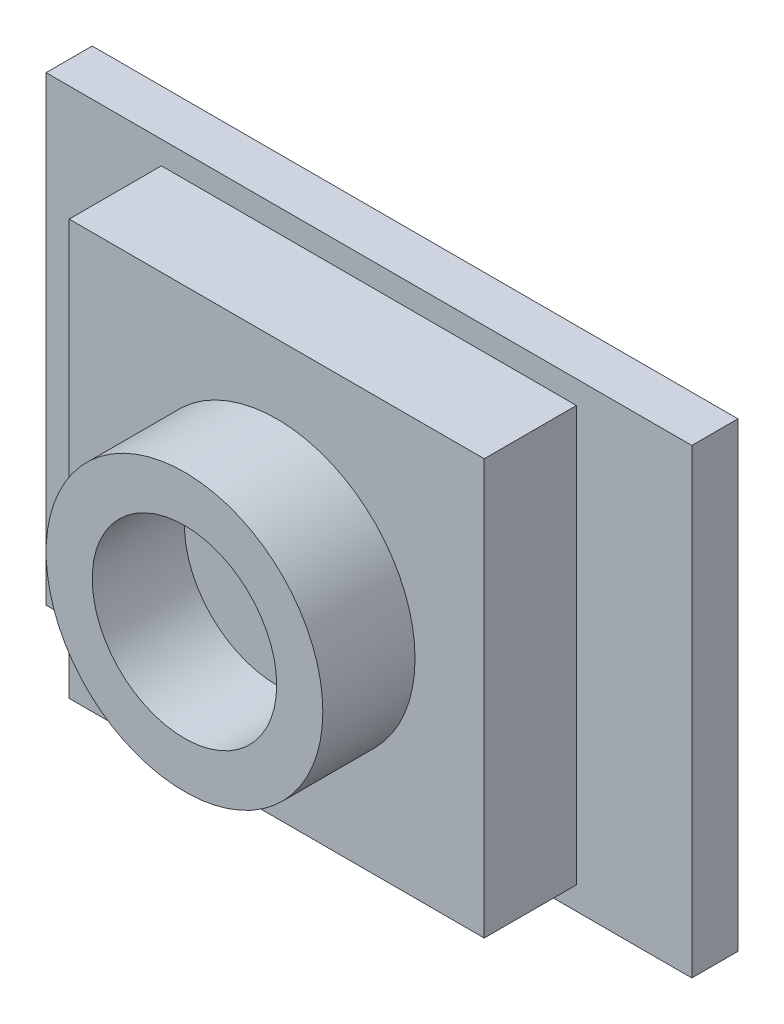
SolidWorks part; units mm, degrees
ref_plane "Front Plane" through (0, 0, 0) normal (0, 0, 1) x (1, 0, 0)
ref_plane "Top Plane" through (0, 0, 0) normal (0, 1, 0) x (1, 0, 0)
ref_plane "Right Plane" through (0, 0, 0) normal (1, 0, 0) x (0, 0, -1)
sketch "Sketch1" plane through (0, 0, 0) normal (0, 0, 1) x (1, 0, 0)
  line L1 (-44.45, -31.75) -> (44.45, -31.75)
  line L2 (-44.45, -31.75) -> (-44.45, 31.75)
  line L3 (-44.45, 31.75) -> (44.45, 31.75)
  line L4 (44.45, -31.75) -> (44.45, 31.75)
  line L5 (-44.45, -31.75) -> (44.45, 31.75) construction
  line L6 (-44.45, 31.75) -> (44.45, -31.75) construction
  line L7 (-28.575, -28.575) -> (28.575, -28.575)
  line L8 (-28.575, -28.575) -> (-28.575, 28.575)
  line L9 (-28.575, 28.575) -> (28.575, 28.575)
  line L10 (28.575, -28.575) -> (28.575, 28.575)
  line L11 (-28.575, -28.575) -> (28.575, 28.575) construction
  line L12 (-28.575, 28.575) -> (28.575, -28.575) construction
  circle A0 centre (0, 0) radius 12.7
  circle A1 centre (0, 0) radius 19.05
  point P0 (0, 0)
  dimension "D3" = 25.4
  dimension "D4" = 38.1
  dimension "D1" = 88.9
  dimension "D2" = 63.5
  dimension "D5" = 57.15
  dimension "D6" = 57.15
sketch "Sketch2" plane through (0, 0, 0) normal (0, 0, 1) x (1, 0, 0)
  line L0 (-44.45, -31.75) -> (-44.45, 31.75) construction
  line L1 (-44.45, 31.75) -> (44.45, 31.75) construction
  line L2 (44.45, -31.75) -> (44.45, 31.75) construction
  line L3 (-44.45, -31.75) -> (44.45, -31.75) construction
  line L4 (-44.45, -31.75) -> (-44.45, 31.75)
  line L5 (-44.45, 31.75) -> (44.45, 31.75)
  line L6 (44.45, -31.75) -> (44.45, 31.75)
  line L7 (-44.45, -31.75) -> (44.45, -31.75)
extrude "Boss-Extrude1" add sketch "Sketch2" against normal blind 6.35
sketch "Sketch3" plane through (0, 0, 0) normal (0, 0, 1) x (1, 0, 0)
  line L0 (-28.575, -28.575) -> (-28.575, 28.575) construction
  line L1 (-28.575, 28.575) -> (28.575, 28.575) construction
  line L2 (28.575, -28.575) -> (28.575, 28.575) construction
  line L3 (-28.575, -28.575) -> (28.575, -28.575) construction
  line L4 (-28.575, -28.575) -> (-28.575, 28.575)
  line L5 (-28.575, 28.575) -> (28.575, 28.575)
  line L6 (28.575, -28.575) -> (28.575, 28.575)
  line L7 (-28.575, -28.575) -> (28.575, -28.575)
extrude "Boss-Extrude2" add sketch "Sketch3" along normal blind 12.7
ref_plane "Plane1" through (0, 0, 12.7) normal (0, 0, 1) x (1, 0, 0)
sketch "Sketch4" plane through (0, 0, 12.7) normal (0, 0, 1) x (1, 0, 0)
  circle A0 centre (0, 0) radius 19.05 construction
  circle A1 centre (0, 0) radius 12.7 construction
  circle A2 centre (0, 0) radius 19.05
  circle A3 centre (0, 0) radius 12.7
extrude "Boss-Extrude3" add sketch "Sketch4" along normal blind 12.7
